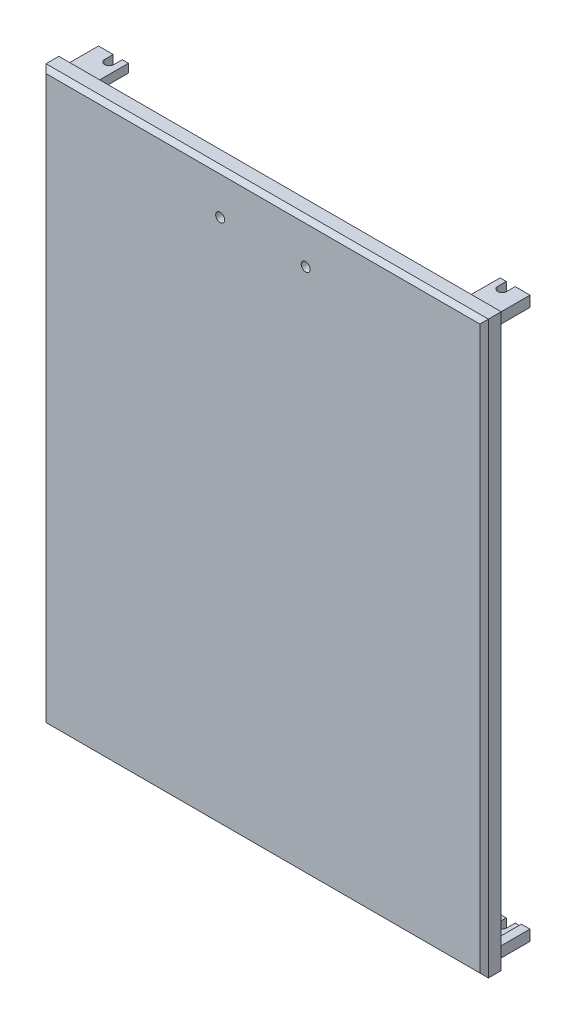
SolidWorks part; units mm, degrees
ref_plane "Front Plane" through (0, 0, 0) normal (0, 0, 1) x (1, 0, 0)
ref_plane "Top Plane" through (0, 0, 0) normal (0, 1, 0) x (1, 0, 0)
ref_plane "Right Plane" through (0, 0, 0) normal (1, 0, 0) x (0, 0, -1)
sketch "Sketch1" plane through (0, 0, 0) normal (0, 0, 1) x (1, 0, 0)
  line L1 (-103.5, -133.5) -> (103.5, -133.5)
  line L2 (-103.5, -133.5) -> (-103.5, 133.5)
  line L3 (-103.5, 133.5) -> (103.5, 133.5)
  line L4 (103.5, -133.5) -> (103.5, 133.5)
  line L5 (-103.5, -133.5) -> (103.5, 133.5) construction
  line L6 (-103.5, 133.5) -> (103.5, -133.5) construction
  point P0 (0, 0)
  dimension "D1" = 207
  dimension "D2" = 267
extrude "Boss-Extrude1" add sketch "Sketch1" along normal blind 8
sketch "Sketch2" plane through (0, 0, 0) normal (0, 0, -1) x (-1, 0, 0)
  line L1 (-100.95, -130.95) -> (100.95, -130.95)
  line L2 (-100.95, -130.95) -> (-100.95, 130.95)
  line L3 (-100.95, 130.95) -> (100.95, 130.95)
  line L4 (100.95, -130.95) -> (100.95, 130.95)
  line L5 (-100.95, -130.95) -> (100.95, 130.95) construction
  line L6 (-100.95, 130.95) -> (100.95, -130.95) construction
  point P0 (0, 0)
  dimension "D1" = 201.9
  dimension "D2" = 261.9
extrude "Boss-Extrude2" add sketch "Sketch2" along normal blind 2
sketch "Sketch3" plane through (0, 0, -2) normal (0, 0, -1) x (-1, 0, 0)
  line L0 (86.95, -130.95) -> (86.95, -126.95)
  line L1 (-100.95, -130.95) -> (100.95, -130.95) construction
  line L2 (86.95, -126.95) -> (96.95, -126.95)
  line L3 (96.95, -126.95) -> (96.95, -125.95)
  line L4 (96.95, -125.95) -> (100.95, -125.95)
  line L5 (100.95, -130.95) -> (100.95, 130.95) construction
  line L6 (100.95, -125.95) -> (100.95, -130.95)
  line L7 (100.95, -130.95) -> (86.95, -130.95)
  dimension "D1" = 4
  dimension "D2" = 4
  dimension "D3" = 14
  dimension "D4" = 5
extrude "Boss-Extrude3" add sketch "Sketch3" along normal blind 14
sketch "Sketch4" plane through (0, -126.95, 0) normal (0, 1, 0) x (1, 0, 0)
  line L0 (-91.95, 16) -> (-91.95, 12) construction
  line L1 (-96.95, 16) -> (-86.95, 16) construction
  line L2 (-89.85, 16) -> (-89.85, 12)
  line L3 (-94.05, 16) -> (-94.05, 12)
  arc A0 (-89.85, 16) -> (-94.05, 16) centre (-91.95, 16) ccw
  arc A1 (-94.05, 12) -> (-89.85, 12) centre (-91.95, 12) ccw
  point P4 (-91.95, 14)
  point P9 (-93.95, 13.1278)
  dimension "D1" = 2.1
  dimension "D2" = 4
extrude "Cut-Extrude1" cut sketch "Sketch4" against normal through all
mirror "Mirror1" about plane through (0, 0, 0) normal (0, 1, 0) of "Cut-Extrude1", "Boss-Extrude3" second plane through (0, 0, 0) second plane normal (1, 0, 0)
sketch "Sketch5" plane through (0, 0, -2) normal (0, 0, -1) x (-1, 0, 0)
  line L0 (-20, 113.95) -> (20, 113.95) construction
  line L1 (86.95, 130.95) -> (-86.95, 130.95) construction
  circle A0 centre (-20, 113.95) radius 2.1
  circle A1 centre (20, 113.95) radius 2.1
  point P4 (0, 113.95)
  point P5 (20, 114.1714)
  dimension "D1" = 4.2
  dimension "D2" = 40
  dimension "D3" = 17
extrude "Cut-Extrude2" cut sketch "Sketch5" against normal through all
chamfer "Chamfer1" distance 2 angle 45 4 edges at (0, -133.5, 8) (-103.5, 0, 8) (0, 133.5, 8) (103.5, 0, 8)
equation "\"M4Thru\" = 4 + \"Tol\""
equation "\"Tol\"= 0.2"
equation "\"D1@Sketch4\"=\"M4Thru\"/2"
equation "\"D1@Sketch5\"=\"M4Thru\""
